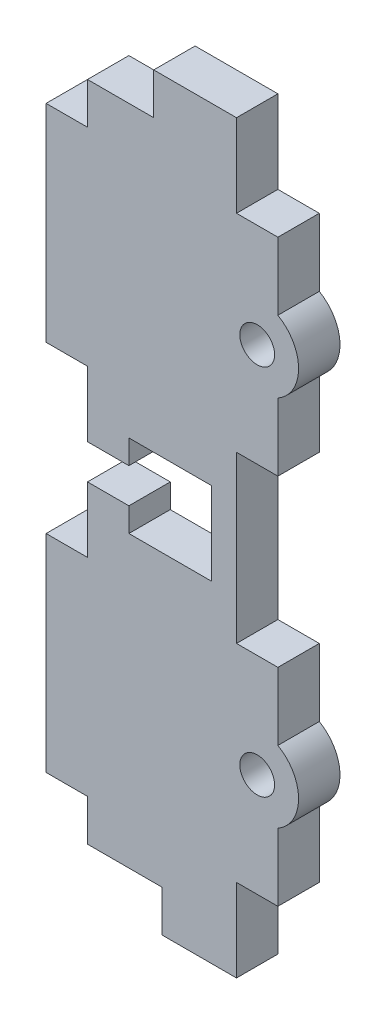
SolidWorks part; units mm, degrees
ref_plane "Front Plane" through (0, 0, 0) normal (0, 0, 1) x (1, 0, 0)
ref_plane "Top Plane" through (0, 0, 0) normal (0, 1, 0) x (1, 0, 0)
ref_plane "Right Plane" through (0, 0, 0) normal (1, 0, 0) x (0, 0, -1)
sketch "Sketch1" plane through (0, 0, 0) normal (0, 0, 1) x (1, 0, 0)
  line L1 (0, 0) -> (-18, 0)
  line L2 (0, 0) -> (0, 80)
  line L3 (0, 80) -> (-18, 80)
  line L4 (-18, 0) -> (-18, 80)
  dimension "D1" = 80
  dimension "D2" = 18
extrude "Boss-Extrude1" add sketch "Sketch1" along normal blind 5
sketch "Sketch2" plane through (0, 0, 0) normal (0, 0, -1) x (-1, 0, 0)
  line L0 (0, 0) -> (0, 80) construction
  line L1 (0, 75) -> (-5, 75)
  line L2 (0, 75) -> (0, 50)
  line L3 (0, 50) -> (-5, 50)
  line L4 (-5, 75) -> (-5, 50)
  line L5 (0, 80) -> (18, 80) construction
  line L6 (18, 0) -> (0, 0) construction
  line L7 (0, 5) -> (-5, 5)
  line L8 (0, 5) -> (0, 30)
  line L9 (0, 30) -> (-5, 30)
  line L10 (-5, 5) -> (-5, 30)
  line L11 (9, 80) -> (9, 72.8232) construction
  line L12 (23, 5) -> (23, 30)
  line L13 (18, 30) -> (23, 30)
  line L14 (18, 5) -> (18, 30)
  line L15 (18, 5) -> (23, 5)
  line L16 (23, 75) -> (23, 50)
  line L17 (18, 50) -> (23, 50)
  line L18 (18, 75) -> (18, 50)
  line L19 (18, 75) -> (23, 75)
  dimension "D1" = 5
  dimension "D2" = 5
  dimension "D3" = 25
  dimension "D4" = 5
  dimension "D5" = 25
  dimension "D6" = 5
extrude "Boss-Extrude2" add sketch "Sketch2" against normal blind 5
sketch "Sketch3" plane through (0, 0, 0) normal (0, -1, 0) x (1, 0, 0)
  line L0 (-18, 5) -> (0, 5) construction
  line L1 (0, 0) -> (-9, 0)
  line L2 (0, 0) -> (0, 5)
  line L3 (0, 5) -> (-9, 5)
  line L4 (-9, 0) -> (-9, 5)
extrude "Boss-Extrude3" add sketch "Sketch3" along normal blind 5
sketch "Sketch4" plane through (0, 0, 0) normal (0, 0, -1) x (-1, 0, 0)
  line L1 (0, 80) -> (10, 80)
  line L2 (0, 80) -> (0, 85)
  line L3 (0, 85) -> (10, 85)
  line L4 (10, 80) -> (10, 85)
  dimension "D1" = 10
  dimension "D2" = 5
extrude "Boss-Extrude4" add sketch "Sketch4" against normal blind 5
sketch "Sketch5" plane through (0, 0, 0) normal (0, 0, -1) x (-1, 0, 0)
  line L0 (-5, 75) -> (-5, 50) construction
  line L1 (0, 40) -> (10.0041, 40) construction
  line L2 (0, 30) -> (0, 50) construction
  circle A0 centre (-2.5, 62.5) radius 2.1
  circle A1 centre (-2.5, 17.5) radius 2.1
  dimension "D1" = 2.5
  dimension "D2" = 4.2
extrude "Cut-Extrude1" cut sketch "Sketch5" against normal blind 5
sketch "Sketch6" plane through (0, 0, 0) normal (0, 0, -1) x (-1, 0, 0)
  line L0 (-5, 75) -> (-5, 50) construction
  line L1 (-5, 66.8301) -> (-5, 58.1699)
  line L2 (0, 40) -> (8.931, 40) construction
  line L3 (0, 30) -> (0, 50) construction
  line L4 (-5, 13.1699) -> (-5, 21.8301)
  arc A0 (-5, 66.8301) -> (-5, 58.1699) centre (-2.5, 62.5) ccw
  arc A1 (-5, 13.1699) -> (-5, 21.8301) centre (-2.5, 17.5) cw
  dimension "D1" = 5
extrude "Boss-Extrude5" add sketch "Sketch6" against normal blind 5
sketch "Sketch7" plane through (0, 0, 5) normal (0, 0, 1) x (1, 0, 0)
  line L0 (-18, 50) -> (-18, 30) construction
  line L1 (-18, 42.1) -> (-13, 42.1)
  line L2 (-18, 42.1) -> (-18, 37.9)
  line L3 (-18, 37.9) -> (-13, 37.9)
  line L4 (-13, 42.1) -> (-13, 37.9)
  line L6 (-13, 45) -> (-3, 45)
  line L7 (-13, 45) -> (-13, 35)
  line L8 (-13, 35) -> (-3, 35)
  line L9 (-3, 45) -> (-3, 35)
  point P10 (-18, 40)
  point P11 (-18, 40)
  point P12 (-3, 40)
  line M31 (-18, 50) -> (-18, 30)
  dimension "D1" = 5
  dimension "D2" = 10
  dimension "D3" = 4.2
  dimension "D4" = 10
extrude "Cut-Extrude2" cut sketch "Sketch7" against normal blind 5 contours L9 L6 L7 L4 L8 | L4 L1 L3 M31
